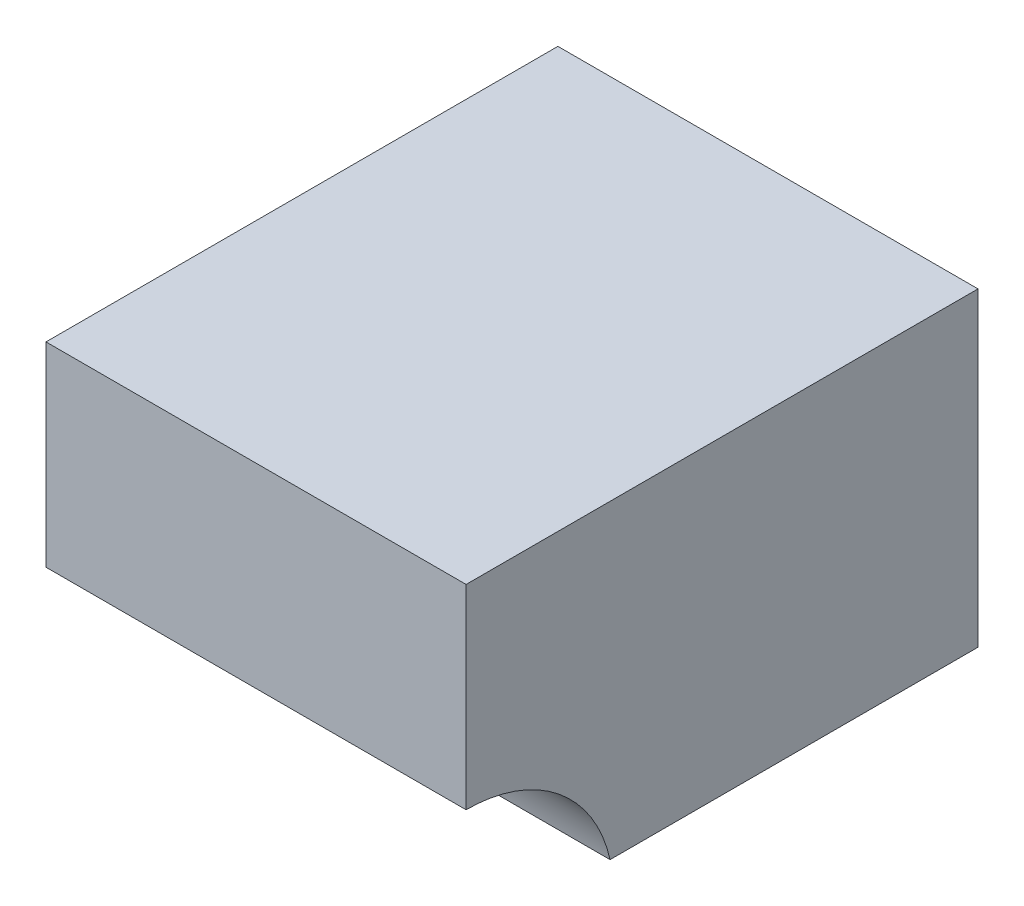
SolidWorks part; units mm, degrees
ref_plane "Front Plane" through (0, 0, 0) normal (0, 0, 1) x (1, 0, 0)
ref_plane "Top Plane" through (0, 0, 0) normal (0, 1, 0) x (1, 0, 0)
ref_plane "Right Plane" through (0, 0, 0) normal (1, 0, 0) x (0, 0, -1)
sketch "Sketch1" plane through (0, 0, 0) normal (1, 0, 0) x (0, 0, -1)
  line L0 (-40.64, 24.638) -> (0, 24.638)
  line L1 (0, 24.638) -> (0, 0)
  line L2 (0, 0) -> (-29.21, 0)
  line L3 (-40.64, 24.638) -> (-40.64, 9.144)
  arc A0 (-29.21, 0) -> (-40.64, 9.144) centre (-40.64, -2.5717) ccw
  dimension "D1" = 24.638
  dimension "D2" = 29.21
  dimension "D3" = 15.494
  dimension "D4" = 40.64
extrude "Boss-Extrude1" add sketch "Sketch1" along normal blind 33.3502
